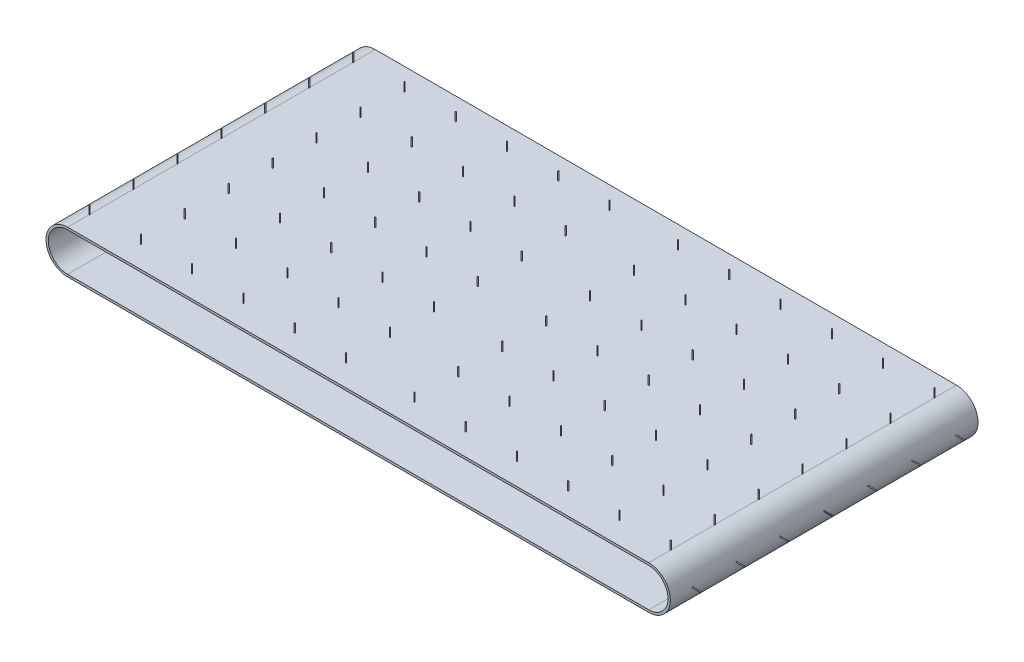
SolidWorks part; units mm, degrees
ref_plane "Front Plane" through (0, 0, 0) normal (0, 0, 1) x (1, 0, 0)
ref_plane "Top Plane" through (0, 0, 0) normal (0, 1, 0) x (1, 0, 0)
ref_plane "Right Plane" through (0, 0, 0) normal (1, 0, 0) x (0, 0, -1)
sketch "Sketch1" plane through (0, 0, 0) normal (0, 0, 1) x (1, 0, 0)
  line L0 (431.8, 0) -> (-431.8, 0) construction
  line L1 (431.8, -28.575) -> (-431.8, -28.575)
  line L2 (431.8, 28.575) -> (-431.8, 28.575)
  line L3 (431.8, -32.004) -> (-431.8, -32.004)
  line L4 (431.8, 32.004) -> (-431.8, 32.004)
  arc A0 (431.8, -28.575) -> (431.8, 28.575) centre (431.8, 0) ccw
  arc A1 (-431.8, 28.575) -> (-431.8, -28.575) centre (-431.8, 0) ccw
  arc A2 (-431.8, 32.004) -> (-431.8, -32.004) centre (-431.8, 0) ccw
  arc A3 (431.8, -32.004) -> (431.8, 32.004) centre (431.8, 0) ccw
  point P3 (0, 0)
  dimension "D1" = 28.575
  dimension "D2" = 863.6
  dimension "D3" = 3.429
extrude "Boss-Extrude1" add sketch "Sketch1" along normal mid plane 457.2
sketch "Sketch2" plane through (0, 0, 0) normal (0, 0, 1) x (1, 0, 0)
  line L0 (431.8, 32.004) -> (-431.8, 32.004) construction
  line L3 (-431.8, 32.004) -> (-432.4071, 32.004)
  line L4 (-432.4071, 44.704) -> (-432.4071, 32.004)
  line L5 (-431.8, 42.9869) -> (-431.8, 26.4208) construction
  line L6 (-431.8, 44.704) -> (-431.8, 32.004)
  line L7 (-432.4071, 44.704) -> (-431.8, 44.704)
  dimension "D1" = 0.6071
  dimension "D2" = 12.7
revolve "Revolve1" add sketch "Sketch2" angle 360 about L5
pattern_linear "LPattern1" count 4 spacing 65.278 along (0, 0, -1) of "Revolve1"
pattern_linear "LPattern4" count 6 spacing 76.2 along (1, 0, 0) of "LPattern1", "Revolve1"
mirror "Mirror1" about plane through (0, 0, 0) normal (0, 0, 1) of "LPattern4", "LPattern1", "Revolve1"
mirror "Mirror2" about plane through (0, 0, 0) normal (1, 0, 0) of "Mirror1", "LPattern4", "LPattern1", "Revolve1"
mirror "Mirror3" about plane through (0, 0, 0) normal (0, 1, 0) of "Mirror2", "Mirror1", "LPattern4", "LPattern1", "Revolve1"
sketch "Sketch4" plane through (0, 0, 0) normal (0, 0, 1) x (1, 0, 0)
  line L0 (434.1707, 0) -> (512.4663, 0) construction
  line L5 (463.7982, 0) -> (476.4982, 0)
  line L6 (463.7982, 0) -> (463.7982, -0.6071)
  line L7 (463.7982, -0.6071) -> (476.4982, -0.6071)
  line L8 (476.4982, 0) -> (476.4982, -0.6071)
  line L9 (55, 0) -> (-55, 0) construction
  arc A2 (431.8, -32.004) -> (431.8, 32.004) centre (431.8, 0) ccw construction
  dimension "D1" = 12.7
  dimension "D2" = 0.6071
revolve "Revolve2" add sketch "Sketch4" angle 360 about L0
pattern_linear "LPattern9" count 4 spacing 65.278 along (0, 0, -1) of "Revolve2"
mirror "Mirror4" about plane through (0, 0, 0) normal (0, 0, 1) of "LPattern9", "Revolve2"
mirror "Mirror5" about plane through (0, 0, 0) normal (1, 0, 0) of "Mirror4", "LPattern9", "Revolve2"
equation "\"D2@Sketch1\"=(3ft)-(2in)"
equation "\"D2@Sketch4\"=(0.0478in)/(2)"
